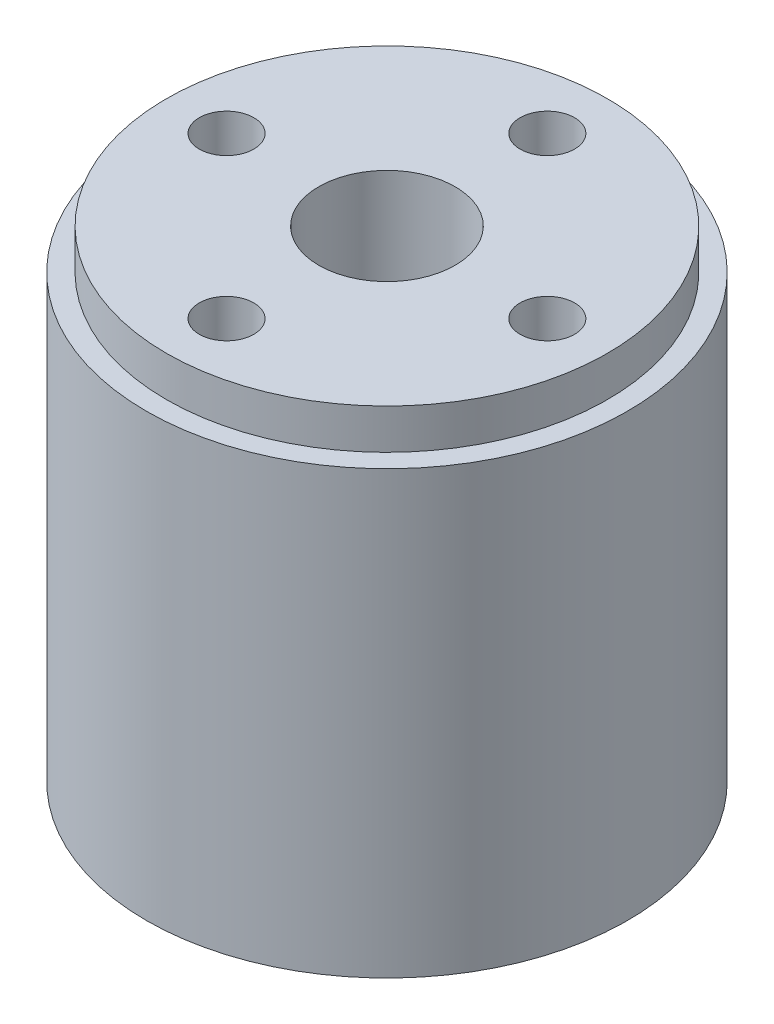
SolidWorks part; units mm, degrees
ref_plane "Front Plane" through (0, 0, 0) normal (0, 0, 1) x (1, 0, 0)
ref_plane "Top Plane" through (0, 0, 0) normal (0, 1, 0) x (1, 0, 0)
ref_plane "Right Plane" through (0, 0, 0) normal (1, 0, 0) x (0, 0, -1)
sketch "Sketch1" plane through (0, 0, 0) normal (0, 1, 0) x (1, 0, 0)
  line L0 (0, 0) -> (0, 41406.0778) construction
  line L1 (0, 0) -> (-41406.0778, 0) construction
  circle A0 centre (0, 0) radius 30
  circle A1 centre (0, 0) radius 8.5
  circle A2 centre (-20, 0) radius 3.4
  circle A3 centre (0, 20) radius 3.4
  circle A4 centre (20, 0) radius 3.4
  circle A5 centre (0, -20) radius 3.4
  point P19 (0, 0)
  dimension "D1" = 60
  dimension "D2" = 17
  dimension "D3" = 6.8
  dimension "D4" = 20
  dimension "D5" = 4
extrude "Boss-Extrude1" add sketch "Sketch1" along normal blind 60
sketch "Sketch3" plane through (0, 60, 0) normal (0, 1, 0) x (1, 0, 0)
  circle A0 centre (0, 0) radius 27.5
  circle A1 centre (0, 0) radius 30
  dimension "D1" = 55
extrude "Cut-Extrude1" cut sketch "Sketch3" against normal blind 5
chamfer "Chamfer1" distance 5 angle 45 1 edges at (0, 0, 8.5)
